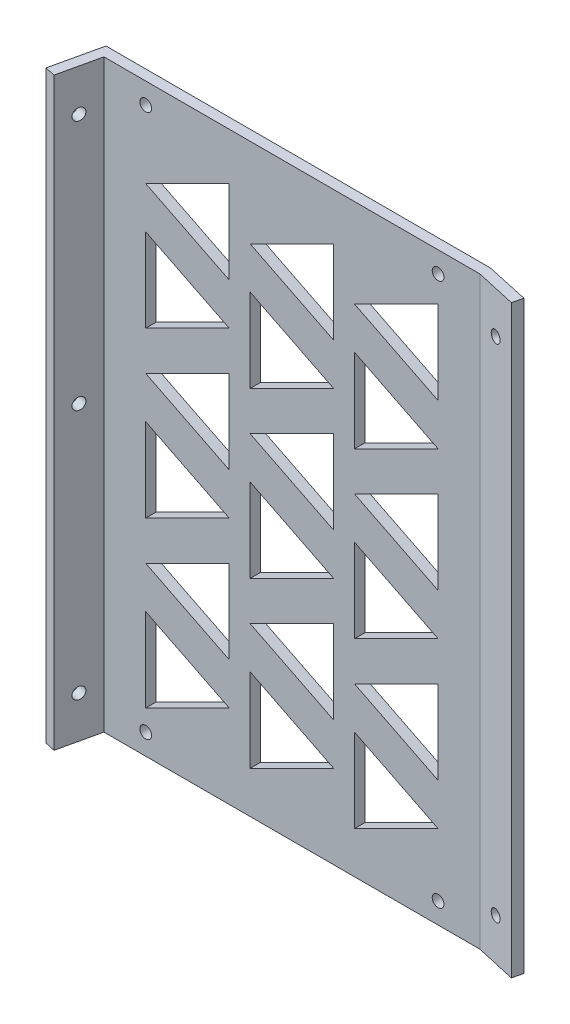
SolidWorks part; units mm, degrees
material "Copper"
ref_plane "Front Plane" through (0, 0, 0) normal (0, 0, 1) x (1, 0, 0)
ref_plane "Top Plane" through (0, 0, 0) normal (0, 1, 0) x (1, 0, 0)
ref_plane "Right Plane" through (0, 0, 0) normal (1, 0, 0) x (0, 0, -1)
sketch "Sketch1" plane through (0, 0, 0) normal (0, 0, 1) x (1, 0, 0)
  line L1 (0, 0) -> (-114.3, 0)
  line L2 (0, 0) -> (0, -177.8)
  line L3 (0, -177.8) -> (-114.3, -177.8)
  line L4 (-114.3, 0) -> (-114.3, -177.8)
  dimension "D1" = 177.8
  dimension "D2" = 114.3
extrude "Boss-Extrude1" add sketch "Sketch1" along normal blind 3.175
sketch "Sketch2" plane through (0, -177.8, 0) normal (0, -1, 0) x (1, 0, 0)
  line L0 (-114.3, 3.175) -> (-117.0878, 15.5652)
  line L1 (-117.0878, 15.5652) -> (-120.1854, 14.8683)
  line L2 (-120.1854, 14.8683) -> (-116.84, 0)
  line L3 (-116.84, 0) -> (-114.3, 0)
  line L4 (-114.3, 3.175) -> (-114.3, 0) construction
  line L9 (-114.3, 3.175) -> (-114.3, 0)
  line L10 (0, 3.175) -> (0, 0)
  line L11 (0, 3.175) -> (12.3902, 5.9628)
  line L12 (12.3902, 5.9628) -> (13.0872, 2.8652)
  line L13 (13.0872, 2.8652) -> (0, 0)
  dimension "D1" = 12.7
  dimension "D2" = 3.175
  dimension "D3" = 12.7
  dimension "D4" = 3.175
  dimension "D6" = 2.54
extrude "Boss-Extrude2" add sketch "Sketch2" against normal blind 177.8
sketch "Sketch3" plane through (-108.1124, 0, -24.3253) normal (0.9756, 0, 0.2195) x (0.2195, 0, -0.9756)
  line L0 (-40.8878, 0) -> (-40.8878, -177.8) construction
  line L1 (-28.1878, 0) -> (-40.8878, 0) construction
  circle A0 centre (-34.5378, -165.1) radius 1.778
  circle A1 centre (-34.5378, -88.9) radius 1.778
  circle A2 centre (-34.5378, -12.7) radius 1.778
  dimension "D1" = 3.556
  dimension "D2" = 3.556
  dimension "D3" = 3.556
  dimension "D4" = 6.35
  dimension "D5" = 6.35
  dimension "D6" = 6.35
  dimension "D7" = 152.4
  dimension "D8" = 12.7
  dimension "D9" = 76.2
extrude "Cut-Extrude1" cut sketch "Sketch3" against normal blind 203.2
sketch "Sketch4" plane through (0, 0, 3.175) normal (0, 0, 1) x (1, 0, 0)
  line L0 (-101.6, -165.1) -> (-101.6, -139.7)
  line L1 (-101.6, -139.7) -> (-76.2, -152.4)
  line L2 (-76.2, -152.4) -> (-101.6, -165.1)
  line L3 (-101.6, -127) -> (-76.2, -139.7)
  line L4 (-76.2, -139.7) -> (-76.2, -114.3)
  line L5 (-76.2, -114.3) -> (-101.6, -127)
  line L6 (-114.3, -177.8) -> (0, -177.8) construction
  line L7 (-114.3, 0) -> (-114.3, -177.8) construction
  dimension "D1" = 25.4
  dimension "D2" = 25.4
  dimension "D3" = 12.7
  dimension "D4" = 12.7
  dimension "D5" = 25.4
  dimension "D6" = 12.7
  dimension "D7" = 25.4
  dimension "D8" = 25.4
  dimension "D9" = 12.7
  dimension "D10" = 12.7
extrude "Cut-Extrude2" cut sketch "Sketch4" against normal blind 3.175
pattern_linear "LPattern2" count 3 spacing 50 along (0, 1, 0) of "Cut-Extrude2"
pattern_linear "LPattern3" count 3 spacing 31.75 along (1, 0, 0) of "LPattern2", "Cut-Extrude2"
sketch "Sketch5" plane through (0, 0, 3.175) normal (0, 0, 1) x (1, 0, 0)
  line L0 (-114.3, -177.8) -> (0, -177.8) construction
  line L1 (0, -177.8) -> (0, 0) construction
  line L2 (0, 0) -> (-114.3, 0) construction
  circle A0 centre (-101.6, -171.45) radius 1.778
  circle A1 centre (-12.7, -171.45) radius 1.778
  circle A2 centre (-12.7, -6.35) radius 1.778
  circle A3 centre (-101.6, -6.35) radius 1.778
  dimension "D1" = 88.9
  dimension "D2" = 3.556
  dimension "D3" = 3.556
  dimension "D4" = 6.35
  dimension "D5" = 6.35
  dimension "D7" = 3.556
  dimension "D8" = 3.556
  dimension "D12" = 12.7
  dimension "D6" = 12.7
  dimension "D9" = 6.35
  dimension "D10" = 6.35
  dimension "D11" = 88.9
extrude "Cut-Extrude3" cut sketch "Sketch5" against normal blind 3.175
sketch "Sketch6" plane through (-0.68, 0, 3.022) normal (-0.2195, 0, 0.9756) x (0.9756, 0, 0.2195)
  line L0 (13.397, -177.8) -> (0.697, -177.8) construction
  line L1 (13.397, 0) -> (13.397, -177.8) construction
  line L2 (13.397, 0) -> (0.697, 0) construction
  circle A0 centre (7.047, -165.1) radius 1.778
  circle A1 centre (7.047, -12.7) radius 1.778
  dimension "D1" = 3.556
  dimension "D2" = 3.556
  dimension "D5" = 12.7
  dimension "D3" = 12.7
  dimension "D4" = 6.35
  dimension "D6" = 6.35
extrude "Cut-Extrude4" cut sketch "Sketch6" against normal blind 3.175
